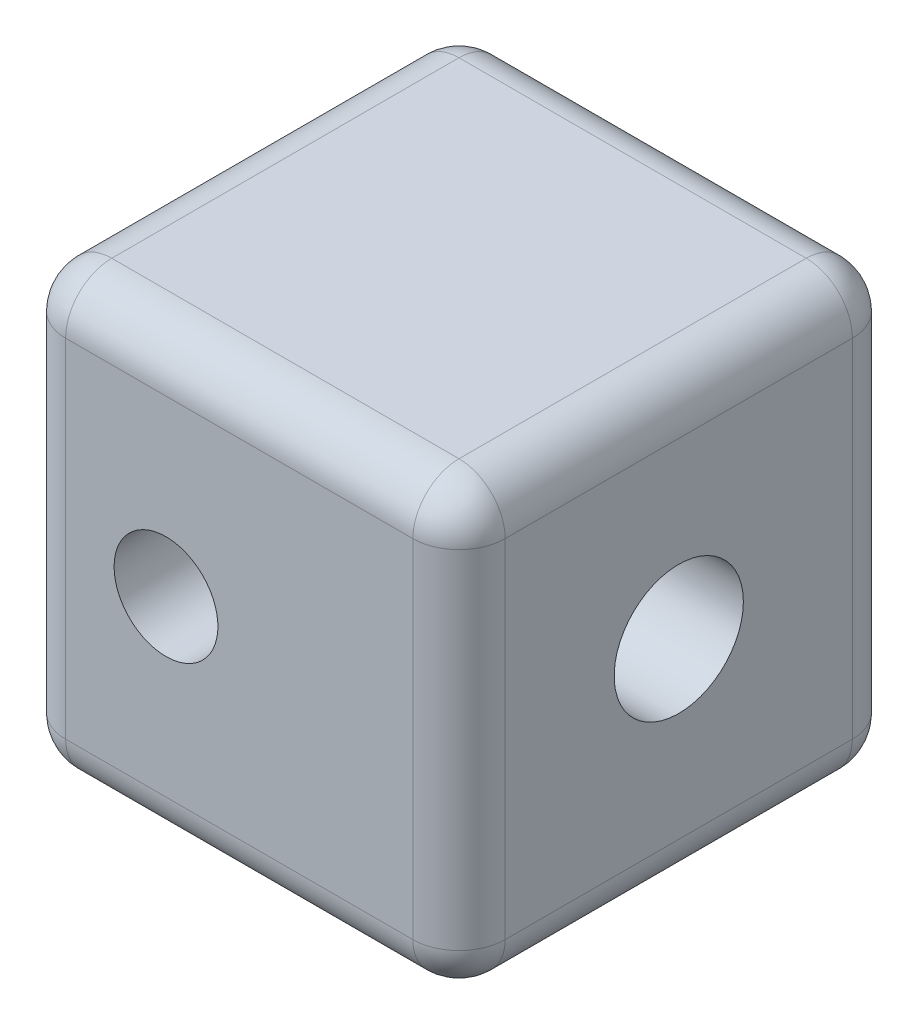
SolidWorks part; units mm, degrees
ref_plane "Front Plane" through (0, 0, 0) normal (0, 0, 1) x (1, 0, 0)
ref_plane "Top Plane" through (0, 0, 0) normal (0, 1, 0) x (1, 0, 0)
ref_plane "Right Plane" through (0, 0, 0) normal (1, 0, 0) x (0, 0, -1)
sketch "Sketch1" plane through (0, 0, 0) normal (1, 0, 0) x (0, 0, -1)
  line L1 (9.525, -9.525) -> (-9.525, -9.525)
  line L2 (9.525, -9.525) -> (9.525, 9.525)
  line L3 (9.525, 9.525) -> (-9.525, 9.525)
  line L4 (-9.525, -9.525) -> (-9.525, 9.525)
  line L5 (9.525, -9.525) -> (-9.525, 9.525) construction
  line L6 (9.525, 9.525) -> (-9.525, -9.525) construction
  circle A0 centre (0, 0) radius 6.35
  dimension "D1" = 12.7
  dimension "D2" = 19.05
extrude "Boss-Extrude1" add sketch "Sketch1" along normal blind 12.7
sketch "Sketch3" plane through (12.7, 0, 0) normal (1, 0, 0) x (0, 0, -1)
  line L4 (-9.525, 9.525) -> (-9.525, -9.525)
  line L5 (-9.525, -9.525) -> (9.525, -9.525)
  line L6 (9.525, -9.525) -> (9.525, 9.525)
  line L7 (9.525, 9.525) -> (-9.525, 9.525)
  line L8 (-9.525, 9.525) -> (-9.525, -9.525)
  line L9 (-9.525, -9.525) -> (9.525, -9.525)
  line L10 (9.525, -9.525) -> (9.525, 9.525)
  line L11 (9.525, 9.525) -> (-9.525, 9.525)
  dimension "D1" = 0
extrude "Boss-Extrude2" add sketch "Sketch3" along normal blind 6.35
sketch "Sketch6" plane through (12.7, 0, 0) normal (-1, 0, 0) x (0, 0, 1)
  circle A0 centre (0, 0) radius 4.6
  circle A1 centre (0, 0) radius 6.35 construction
  dimension "D1" = 1.75
sketch "Sketch5" plane through (19.05, 0, 0) normal (1, 0, 0) x (0, 0, -1)
  circle A0 centre (0, 0) radius 2.8
  dimension "D1" = 5.6
extrude "Cut-Extrude1" cut sketch "Sketch5" against normal blind 7
extrude "Boss-Extrude4" add sketch "Sketch6" along normal up to surface (12.7 mm away) contours A0 up to face at (0, 0, 0)
sketch "Sketch8" plane through (0, 0, -9.525) normal (0, 0, -1) x (-1, 0, 0)
  line L0 (-12.7, -4.6) -> (-12.7, 4.6) construction
  line L1 (-12.7, -4.6) -> (-12.7, 4.6)
  line L2 (-12.7, 0) -> (0, 0)
  line L3 (0, -9.525) -> (0, 9.525) construction
  circle A0 centre (-6.35, 0) radius 2.25
  dimension "D1" = 4.5
extrude "Cut-Extrude2" cut sketch "Sketch8" against normal blind 55 contours L2 A0 | L2 A0
fillet "Fillet1" radius 1 2 edges at (0, 0, -4.6) (0, 0, -6.35)
fillet "Fillet2" radius 2 12 edges at (9.525, -9.525, 9.525) (19.05, -9.525, 0) (9.525, -9.525, -9.525) (0, -9.525, 0) (9.525, 9.525, -9.525) (19.05, 9.525, 0) (9.525, 9.525, 9.525) (0, 9.525, 0) (19.05, 0, 9.525) (0, 0, 9.525) (0, 0, -9.525) (19.05, 0, -9.525)
sketch "Sketch9" plane through (0, 0, -9.525) normal (0, 0, -1) x (-1, 0, 0)
  line L1 (-9.85, 2.0207) -> (-9.85, -2.0207)
  line L2 (-9.85, -2.0207) -> (-6.35, -4.0415)
  line L3 (-6.35, -4.0415) -> (-2.85, -2.0207)
  line L4 (-2.85, -2.0207) -> (-2.85, 2.0207)
  line L5 (-2.85, 2.0207) -> (-6.35, 4.0415)
  line L6 (-6.35, 4.0415) -> (-9.85, 2.0207)
  circle A0 centre (-6.35, 0) radius 2.25 construction
  circle A1 centre (-6.35, 0) radius 2.25
  circle A2 centre (-6.35, 0) radius 3.5 construction
  dimension "D1" = 7
extrude "Cut-Extrude3" cut sketch "Sketch9" against normal blind 2
